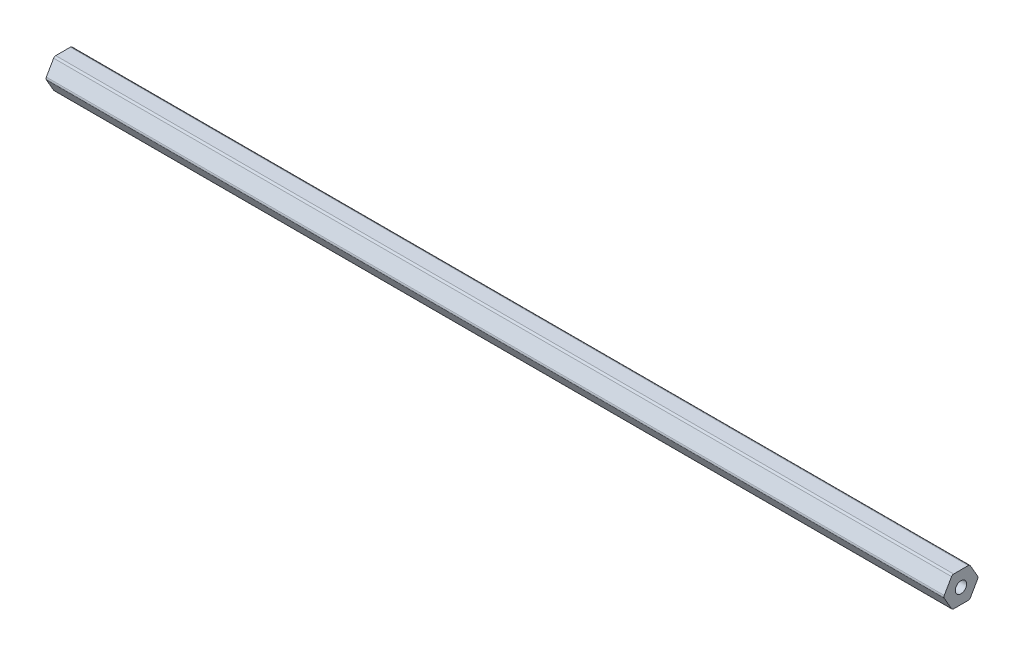
SolidWorks part; units mm, degrees
material "7075-T6 (SN)"
ref_plane "Front Plane" through (0, 0, 0) normal (0, 0, 1) x (1, 0, 0)
ref_plane "Top Plane" through (0, 0, 0) normal (0, 1, 0) x (1, 0, 0)
ref_plane "Right Plane" through (0, 0, 0) normal (1, 0, 0) x (0, 0, -1)
sketch "Sketch1" plane through (0, 0, 0) normal (1, 0, 0) x (0, 0, -1)
  line L1 (7.0391, 0.508) -> (3.9595, 5.842)
  line L2 (3.0796, 6.35) -> (-3.0796, 6.35)
  line L3 (-3.9595, 5.842) -> (-7.0391, 0.508)
  line L4 (-7.0391, -0.508) -> (-3.9595, -5.842)
  line L5 (-3.0796, -6.35) -> (3.0796, -6.35)
  line L6 (3.9595, -5.842) -> (7.0391, -0.508)
  circle A0 centre (0, 0) radius 6.35 construction
  arc A1 (3.0796, 6.35) -> (3.9595, 5.842) centre (3.0796, 5.334) cw
  arc A2 (7.0391, 0.508) -> (7.0391, -0.508) centre (6.1592, 0) cw
  arc A3 (3.9595, -5.842) -> (3.0796, -6.35) centre (3.0796, -5.334) cw
  arc A4 (-3.0796, -6.35) -> (-3.9595, -5.842) centre (-3.0796, -5.334) cw
  arc A5 (-7.0391, -0.508) -> (-7.0391, 0.508) centre (-6.1592, 0) cw
  arc A6 (-3.9595, 5.842) -> (-3.0796, 6.35) centre (-3.0796, 5.334) cw
  circle A7 centre (0, 0) radius 2.3813
  point P11 (3.6662, 6.35)
  point P14 (7.3323, 0)
  dimension "D1" = 12.7
  dimension "D3" = 1.016
  dimension "D4" = 4.7625
  dimension "D2" = 6.35
extrude "Boss-Extrude1" add sketch "Sketch1" along normal blind 377.825
